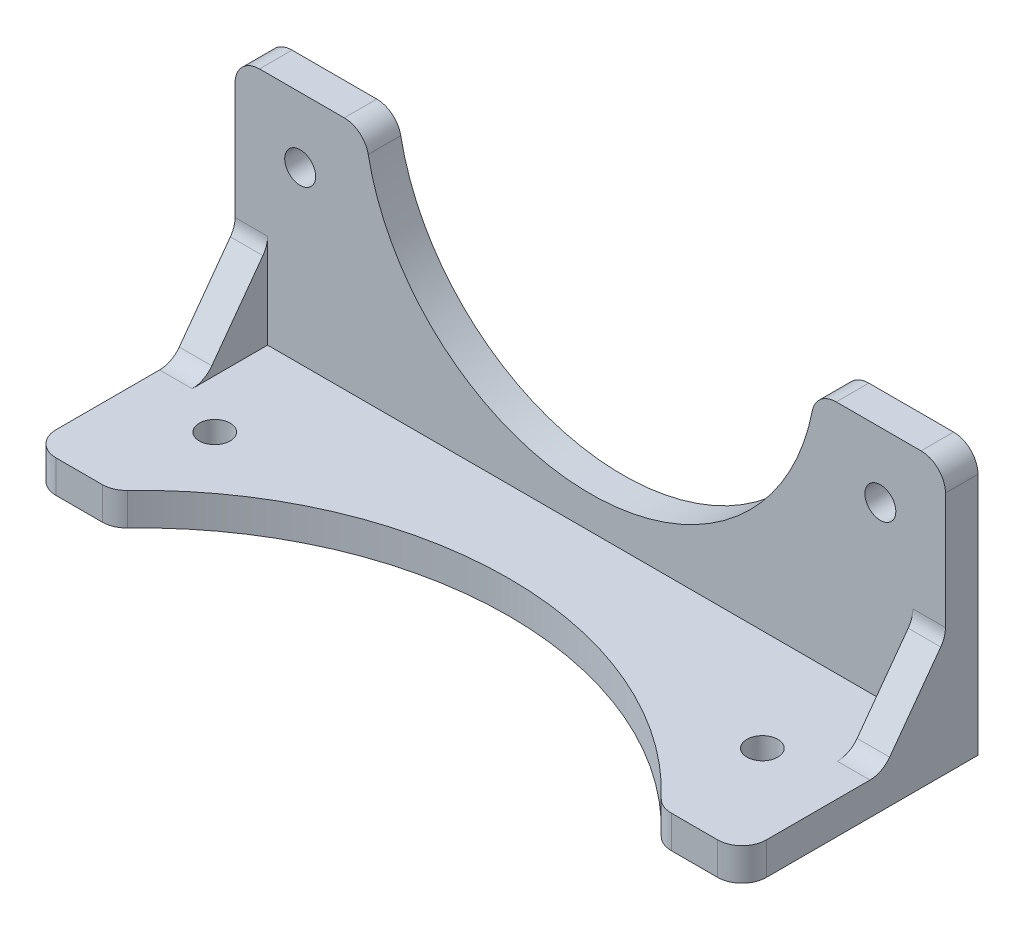
SolidWorks part; units mm, degrees
ref_plane "Спереди" through (0, 0, 0) normal (0, 0, 1) x (1, 0, 0)
ref_plane "Сверху" through (0, 0, 0) normal (0, 1, 0) x (1, 0, 0)
ref_plane "Справа" through (0, 0, 0) normal (1, 0, 0) x (0, 0, -1)
sketch "Sketch1" plane through (0, 0, 0) normal (0, 0, 1) x (1, 0, 0)
  line L0 (-43.65, 4.7838) -> (-27.65, 4.7838)
  line L4 (27.65, 4.7838) -> (43.65, 4.7838)
  line L5 (43.65, 4.7838) -> (43.65, -28.1162)
  line L6 (43.65, -28.1162) -> (-43.65, -28.1162)
  line L7 (-43.65, -28.1162) -> (-43.65, 4.7838)
  line L8 (-40, -0.5162) -> (-40, -5.9162) construction
  line L9 (-40, -3.2162) -> (-31.3, -3.2162) construction
  line L10 (35.65, -3.2162) -> (43.65, -3.2162) construction
  line L12 (35.65, 4.7838) -> (35.65, -3.2162) construction
  line L14 (88.2, -28.1162) -> (-88.2, -28.1162) construction
  line L15 (0, -20.1162) -> (0, -28.1162) construction
  arc A0 (-27.65, 4.7838) -> (27.65, 4.7838) centre (0, 7.6857) ccw
  circle A1 centre (-35.65, -3.2162) radius 1.9
  circle A2 centre (35.65, -3.2162) radius 1.9
  arc A7 (-34, -5.9162) -> (-34, -0.5162) centre (-34, -3.2162) ccw construction
  point P0 (-31.3, -3.2162)
  point P10 (35.65, 4.7838)
  point P18 (-35.65, 4.7838)
  dimension "D2" = 3.8
  dimension "D1" = 16
extrude "Extrude1" add sketch "Sketch1" along normal blind 4
sketch "Sketch2" plane through (0, -28.1162, 0) normal (0, -1, 0) x (1, 0, 0)
  line L0 (-33.65, 29) -> (-43.65, 29)
  line L1 (-43.65, 29) -> (-43.65, 4)
  line L2 (-43.65, 4) -> (43.65, 4)
  line L3 (-43.65, 4) -> (43.65, 4) construction
  line L4 (43.65, 4) -> (43.65, 0) construction
  line L5 (43.65, 4) -> (43.65, 29)
  line L6 (43.65, 29) -> (33.65, 29)
  line L7 (-33.65, 16.5) -> (33.65, 16.5) construction
  line L8 (-33.65, 16.5) -> (-33.65, 29) construction
  line L9 (-33.65, 16.5) -> (-33.65, 4) construction
  line L10 (-43.65, 16.5) -> (-33.65, 16.5) construction
  line L11 (0, 14) -> (0, 4) construction
  arc A0 (-33.65, 29) -> (33.65, 29) centre (0, 59.2441) ccw
  circle A1 centre (-33.65, 16.5) radius 1.9
  circle A2 centre (33.65, 16.5) radius 1.9
  point P16 (0, 16.5)
  dimension "D3" = 3.8
  dimension "D1" = 25
  dimension "D2" = 10
extrude "Extrude2" add sketch "Sketch2" against normal blind 4 separate body
sketch "Sketch3" plane through (43.65, 0, 0) normal (1, 0, 0) x (0, 0, -1)
  line L0 (-4, -24.1162) -> (-11.756, -24.1162)
  line L1 (-4, -24.1162) -> (-29, -24.1162) construction
  line L2 (-11.756, -24.1162) -> (-4, -13.511)
  line L3 (-4, -28.1162) -> (-4, 4.7838) construction
  line L4 (-4, -13.511) -> (-4, -24.1162)
extrude "Extrude3" add sketch "Sketch3" against normal blind 4
mirror "Mirror1" about plane through (0, 0, 0) normal (1, 0, 0) of "Extrude3"
fillet "Fillet1" radius 3 12 edges at (43.65, -26.1162, 29) (33.65, -26.1162, 29) (-33.65, -26.1162, 29) (-43.65, -26.1162, 29) (-41.65, -13.511, 4) (-41.65, -24.1162, 11.756) (41.65, -24.1162, 11.756) (41.65, -13.511, 4) (43.65, 4.7838, 2) (27.65, 4.7838, 2) (-27.65, 4.7838, 2) (-43.65, 4.7838, 2)
equation "\"thickness\"=4"
equation "\"pin_l\"=5"
equation "\"pin_skew\"=4"
equation "\"pin_r\"=5"
equation "\"M4_plastic_thread\"=3.8"
equation "\"M3_plastic_thread\" = 2.8"
equation "\"min_d\"=0.2"
equation "\"D2@Sketch1\"=\"M4_plastic_thread\""
equation "\"D3@Sketch2\"=\"M4_plastic_thread\""
